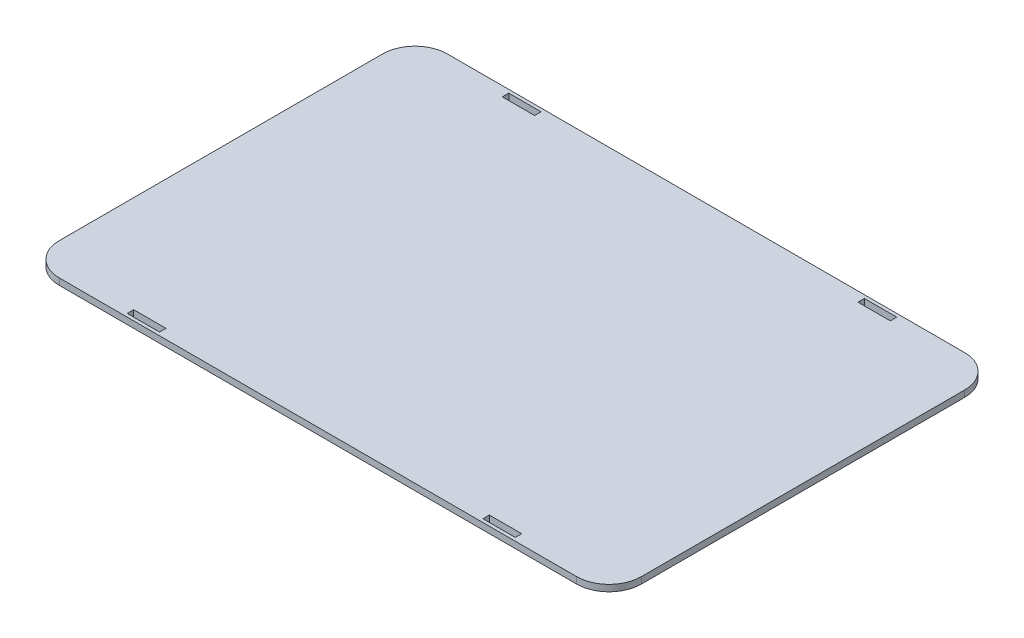
SolidWorks part; units mm, degrees
ref_plane "Front Plane" through (0, 0, 0) normal (0, 0, 1) x (1, 0, 0)
ref_plane "Top Plane" through (0, 0, 0) normal (0, 1, 0) x (1, 0, 0)
ref_plane "Right Plane" through (0, 0, 0) normal (1, 0, 0) x (0, 0, -1)
sketch "Sketch1" plane through (0, 0, 0) normal (0, 1, 0) x (1, 0, 0)
  line L1 (-90, -60) -> (90, -60)
  line L2 (-90, -60) -> (-90, 60)
  line L3 (-90, 60) -> (90, 60)
  line L4 (90, -60) -> (90, 60)
  line L5 (-90, -60) -> (90, 60) construction
  line L6 (-90, 60) -> (90, -60) construction
  point P0 (0, 0)
extrude "Boss-Extrude1" add sketch "Sketch1" along normal blind 2
fillet "Fillet1" radius 10 1 edges at (-90, 1, 60)
fillet "Fillet2" radius 10 1 edges at (-90, 1, -60)
fillet "Fillet3" radius 10 1 edges at (90, 1, 60)
fillet "Fillet4" radius 10 1 edges at (90, 1, -60)
sketch "Sketch2" plane through (0, 0, 0) normal (0, 1, 0) x (1, 0, 0)
  line L0 (-60, 71.1776) -> (-60, -74.4261) construction
  line L1 (-50, 71.1776) -> (-50, -76.5144) construction
  line L2 (50, 71.1776) -> (50, -76.5144) construction
  line L3 (60, 71.1776) -> (60, -76.5144) construction
  line L4 (-90, 50) -> (-90, -50) construction
  line L5 (90, -50) -> (90, 50) construction
  line L6 (-130.0571, 57) -> (120.9097, 57) construction
  line L7 (-130.0571, 59) -> (129.8251, 59) construction
  line L8 (-116.0188, -57) -> (127.8527, -57) construction
  line L9 (-116.0188, -59) -> (127.8537, -59) construction
  line L10 (80, 60) -> (-80, 60) construction
  line L11 (-80, -60) -> (80, -60) construction
  dimension "D1" = 30
  dimension "D2" = 40
  dimension "D3" = 30
  dimension "D4" = 40
  dimension "D5" = 1
  dimension "D6" = 3
  dimension "D7" = 3
  dimension "D8" = 1
sketch "Sketch3" plane through (0, 0, 0) normal (0, 1, 0) x (1, 0, 0)
  line L0 (-60, 71.1776) -> (-60, -74.4261) construction
  line L1 (-60, 59) -> (-50, 59)
  line L2 (-60, 59) -> (-60, 57)
  line L3 (-60, 57) -> (-50, 57)
  line L4 (-50, 59) -> (-50, 57)
  line L5 (-130.0571, 59) -> (129.8251, 59) construction
  line L6 (-50, 71.1776) -> (-50, -76.5144) construction
  line L7 (-130.0571, 57) -> (120.9097, 57) construction
  line L8 (50, 71.1776) -> (50, -76.5144) construction
  line L9 (50, 59) -> (60, 59)
  line L10 (50, 59) -> (50, 57)
  line L11 (50, 57) -> (60, 57)
  line L12 (60, 59) -> (60, 57)
  line L13 (60, 71.1776) -> (60, -76.5144) construction
  line L14 (-116.0188, -57) -> (127.8527, -57) construction
  line L15 (-60, -57) -> (-50, -57)
  line L16 (-60, -57) -> (-60, -59)
  line L17 (-60, -59) -> (-50, -59)
  line L18 (-50, -57) -> (-50, -59)
  line L19 (-116.0188, -59) -> (127.8537, -59) construction
  line L21 (50, -57) -> (60, -57)
  line L22 (50, -57) -> (50, -59)
  line L23 (50, -59) -> (60, -59)
  line L24 (60, -57) -> (60, -59)
extrude "Cut-Extrude1" cut sketch "Sketch3" along normal blind 7
